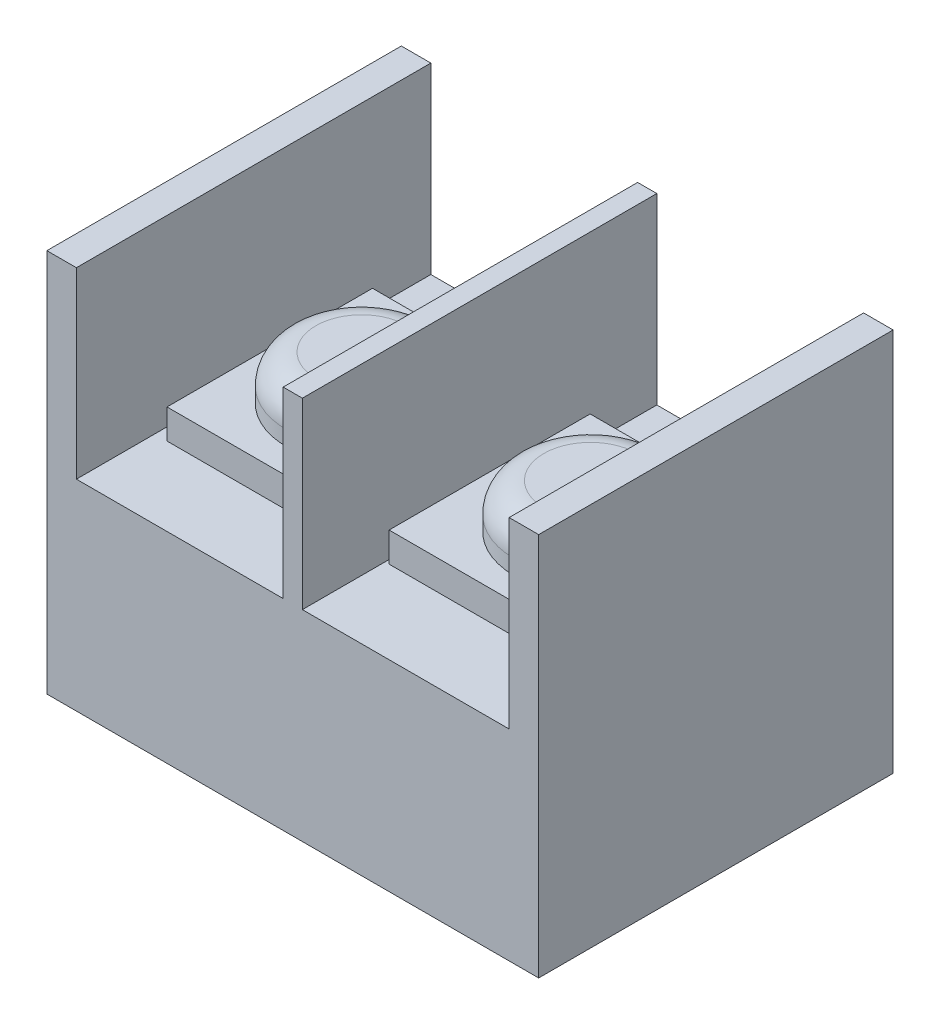
SolidWorks part; units mm, degrees
ref_plane "Front Plane" through (0, 0, 0) normal (0, 0, 1) x (1, 0, 0)
ref_plane "Top Plane" through (0, 0, 0) normal (0, 1, 0) x (1, 0, 0)
ref_plane "Right Plane" through (0, 0, 0) normal (1, 0, 0) x (0, 0, -1)
sketch "Sketch1" plane through (0, 0, 0) normal (0, 1, 0) x (1, 0, 0)
  line L1 (-8.784, 6.6294) -> (7.866, 6.6294)
  line L2 (-8.784, 6.6294) -> (-8.784, -5.3706)
  line L3 (-8.784, -5.3706) -> (7.866, -5.3706)
  line L4 (7.866, 6.6294) -> (7.866, -5.3706)
  dimension "D1" = 16.65
  dimension "D2" = 12
extrude "Boss-Extrude1" add sketch "Sketch1" along normal blind 13
sketch "Sketch2" plane through (0, 0, 5.3706) normal (0, 0, 1) x (1, 0, 0)
  line L0 (7.866, 13) -> (7.866, 0) construction
  line L1 (-7.784, 17.325) -> (-0.784, 17.325)
  line L2 (-7.784, 17.325) -> (-7.784, 6.8)
  line L3 (-7.784, 6.8) -> (-0.784, 6.8)
  line L4 (-0.784, 17.325) -> (-0.784, 6.8)
  line L5 (-0.134, 17.325) -> (6.866, 17.325)
  line L6 (-0.134, 17.325) -> (-0.134, 6.8)
  line L7 (-0.134, 6.8) -> (6.866, 6.8)
  line L8 (6.866, 17.325) -> (6.866, 6.8)
  line L9 (-8.784, 13) -> (-8.784, 0) construction
  line L10 (-8.784, 13) -> (7.866, 13) construction
  dimension "D1" = 1
  dimension "D2" = 1
  dimension "D3" = 7
  dimension "D4" = 7
  dimension "D5" = 6.2
  dimension "D6" = 6.2
extrude "Cut-Extrude1" cut sketch "Sketch2" against normal blind 13
sketch "Sketch3" plane through (0, 6.8, 0) normal (0, 1, 0) x (1, 0, 0)
  line L1 (-7.3682, 4.2378) -> (-1.0125, 4.2378)
  line L2 (-7.3682, 4.2378) -> (-7.3682, -2.7193)
  line L3 (-7.3682, -2.7193) -> (-1.0125, -2.7193)
  line L4 (-1.0125, 4.2378) -> (-1.0125, -2.7193)
  line L5 (0, 4.2378) -> (6.6006, 4.2378)
  line L6 (0, 4.2378) -> (0, -2.5689)
  line L7 (0, -2.5689) -> (6.6006, -2.5689)
  line L8 (6.6006, 4.2378) -> (6.6006, -2.5689)
extrude "Boss-Extrude2" add sketch "Sketch3" along normal blind 1
sketch "Sketch4" plane through (0, 7.8, 0) normal (0, 1, 0) x (1, 0, 0)
  circle A0 centre (-4.1835, 0.6841) radius 2.5464
  circle A1 centre (3.4569, 0.7934) radius 2.5821
extrude "Boss-Extrude3" add sketch "Sketch4" along normal blind 1.5
fillet "Fillet1" radius 1 2 edges at (0.8748, 9.3, -0.7934) (-6.7299, 9.3, -0.6841)
